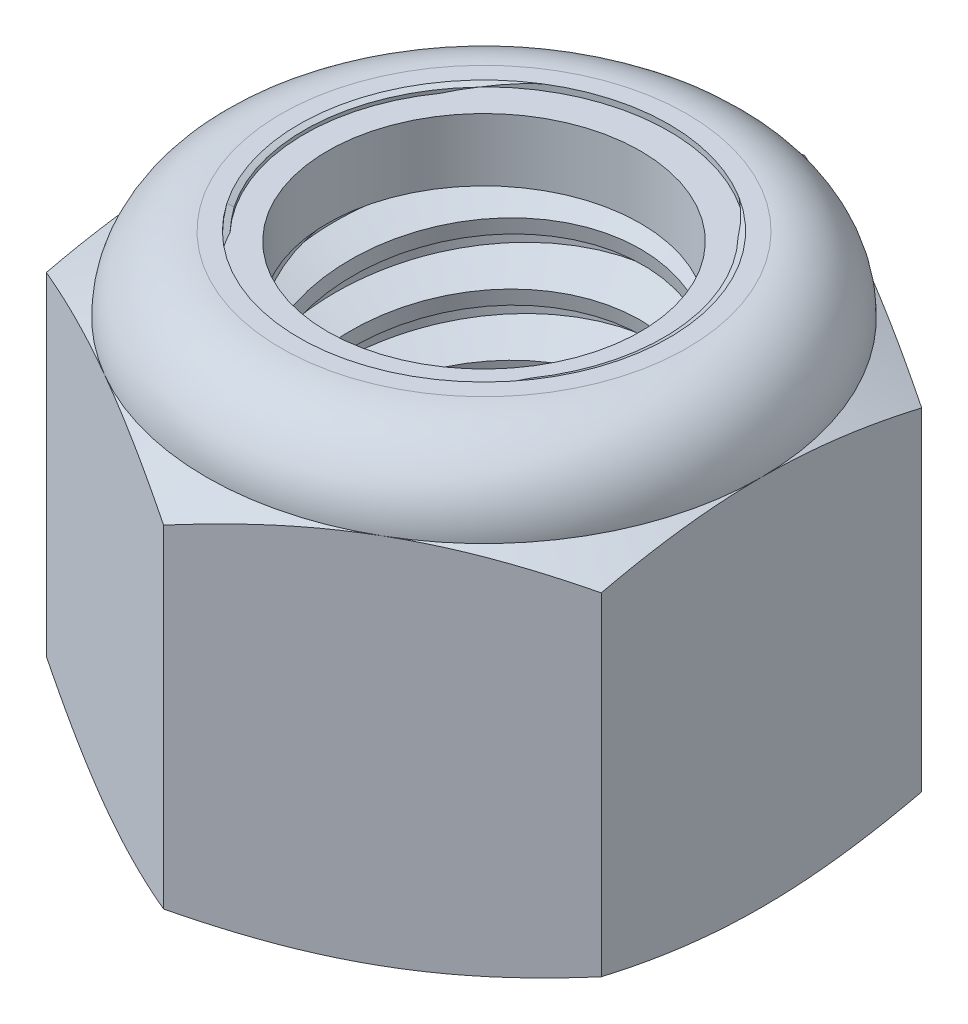
SolidWorks part; units mm, degrees
ref_plane "Front" through (0, 0, 0) normal (0, 0, 1) x (1, 0, 0)
ref_plane "Top" through (0, 0, 0) normal (0, 1, 0) x (1, 0, 0)
ref_plane "Right" through (0, 0, 0) normal (1, 0, 0) x (0, 0, -1)
sketch "Sketch1" plane through (0, 0, 0) normal (0, 1, 0) x (1, 0, 0)
  line L1 (0, 8.2489) -> (-7.1438, 4.1244)
  line L2 (-7.1438, 4.1244) -> (-7.1438, -4.1244)
  line L3 (-7.1438, -4.1244) -> (0, -8.2489)
  line L4 (0, -8.2489) -> (7.1437, -4.1244)
  line L5 (7.1437, -4.1244) -> (7.1437, 4.1244)
  line L6 (7.1437, 4.1244) -> (0, 8.2489)
  circle A0 centre (0, 0) radius 7.1438 construction
  dimension "Hex Flats" = 14.2875
extrude "Extrude1" add sketch "Sketch1" along normal blind 11.5094
sketch "Sketch2" plane through (0, 0, 0) normal (1, 0, 0) x (0, 0, -1)
  line L0 (-4.7625, 0) -> (-4.7625, 11.5094) construction
  line L1 (0, 0) -> (4.7625, 0)
  line L2 (0, 0) -> (0, 11.5094)
  line L3 (0, 11.5094) -> (4.7625, 11.5094)
  line L4 (4.7625, 0) -> (4.7625, 11.5094)
  line L5 (-4.1244, 11.5094) -> (4.1244, 11.5094) construction
  line L7 (0, -4.7625) -> (0, 0) construction
  dimension "Thread Dia" = 9.525
revolve "Revolve1" add sketch "Sketch2" angle 360 about L7
sketch "Sketch3" plane through (0, 0, 0) normal (1, 0, 0) x (0, 0, -1)
  line L0 (4.7625, 11.5094) -> (-4.7625, 11.5094) construction
  line L1 (-4.7625, 11.5094) -> (-4.7625, 9.9219) construction
  line L2 (-4.7625, 9.9219) -> (4.7625, 11.5094) construction
  line L3 (4.7625, 11.5094) -> (4.7951, 11.3136) construction
  line L4 (4.7951, 11.3136) -> (5.0235, 9.9435)
  line L5 (5.0235, 9.9435) -> (4.0944, 10.2916)
  line L6 (4.0944, 10.2916) -> (4.0291, 10.683)
  line L7 (4.0291, 10.683) -> (4.7951, 11.3136)
  line L8 (4.0617, 10.4873) -> (4.9093, 10.6286) construction
  line L9 (4.7625, 11.5094) -> (4.7625, 10.6041) construction
  line L10 (4.7625, 10.6041) -> (-4.7625, 9.0166) construction
  line L11 (-4.7625, 9.0166) -> (-4.7625, 9.9219) construction
  line L12 (-0.2832, 11.5094) -> (0.2832, 8.1113) construction
  line L13 (-4.7625, 0) -> (-4.7625, 11.5094) construction
  line L14 (0, 11.5094) -> (4.7625, 11.5094) construction
  line L15 (4.7625, 0) -> (4.7625, 11.5094) construction
  point P13 (0, 9.8103)
  dimension "D1" = 0.1984
  dimension "D2" = 0.3969
  dimension "Thread Pitch" = 1.5875
  dimension "D4" = 60
  dimension "D5" = 1.5875
revolve "Cut-Revolve1" cut sketch "Sketch3" angle 360 about L12
pattern_linear "LPattern1" count 7 spacing 1.5875 along (0, -1, 0) count 2 spacing 1.5875 along (0, 1, 0) of "Cut-Revolve1"
sketch "Sketch4" plane through (0, 0, 0) normal (1, 0, 0) x (0, 0, -1)
  line L0 (0, 11.5094) -> (4.7625, 11.5094)
  line L1 (4.7625, 11.5094) -> (4.0291, 11.1674)
  line L2 (4.0291, 11.1674) -> (4.0291, 0.342)
  line L3 (4.0291, 0.342) -> (4.7625, 0)
  line L4 (4.7625, 0) -> (0, 0)
  line L5 (0, 0) -> (0, 11.5094)
  line L6 (4.7625, 0) -> (4.7625, 11.5094) construction
  line L7 (0, 11.5094) -> (4.7625, 11.5094) construction
  line L8 (0, 0) -> (4.7625, 0) construction
  line L9 (0, 0) -> (0, 11.5094) construction
  line L10 (0, 11.5094) -> (0, 12.3186) construction
  dimension "D1" = 25
revolve "Cut-Revolve2" cut sketch "Sketch4" angle 360 about L10
combine bodies "Combine1" operation type subtract main body 112 bodies to subtract 111
sketch "Sketch5" plane through (0, 0, 0) normal (1, 0, 0) x (0, 0, -1)
  line L0 (0, 0) -> (7.1438, 0)
  line L1 (7.1438, 0) -> (8.2489, 0.5153)
  line L2 (8.2489, 0.5153) -> (8.2489, 9.0758)
  line L3 (8.2489, 9.0758) -> (7.1437, 9.5911)
  line L4 (5.2255, 11.5094) -> (5.2255, 12.7794)
  line L5 (5.2255, 12.7794) -> (9.5189, 12.7794)
  line L6 (9.5189, 12.7794) -> (9.5189, -1.27)
  line L7 (9.5189, -1.27) -> (0, -1.27)
  line L8 (0, -1.27) -> (0, 0)
  line L9 (7.1437, 9.5911) -> (7.1438, 0) construction
  line L10 (0, 0) -> (4.7625, 0) construction
  line L13 (8.2489, 4.7956) -> (9.5189, 4.7956) construction
  line L14 (8.2489, 11.5094) -> (8.2489, 0) construction
  line L15 (0, 0) -> (0, 12.7794) construction
  line L20 (0, 12.7794) -> (5.2255, 12.7794) construction
  line L22 (0, 11.5094) -> (4.7625, 11.5094) construction
  arc A0 (7.1437, 9.5911) -> (5.2255, 11.5094) centre (5.2255, 9.5911) ccw
  dimension "D1" = 25
  dimension "D2" = 1.27
  dimension "D3" = 11.5094
  dimension "D4" = 1.9182
revolve "Cut-Revolve3" cut sketch "Sketch5" angle 360 about L15
sketch "Sketch6" plane through (0, 0, 0) normal (1, 0, 0) x (0, 0, -1)
  line L0 (0, 9.5911) -> (6.9914, 9.5911)
  line L1 (5.2255, 11.357) -> (4.6273, 11.357)
  line L2 (0, 12.7794) -> (0, 9.5911)
  line L3 (4.6273, 12.7794) -> (0, 12.7794)
  line L4 (0, 12.7794) -> (5.2255, 12.7794) construction
  line L5 (0, 0) -> (0, 12.7794) construction
  line L6 (0, 12.7794) -> (0, 44.323) construction
  line L7 (4.6273, 11.357) -> (4.6273, 12.7794)
  line L8 (5.2255, 11.5094) -> (5.2255, 11.357) construction
  line L9 (4.6273, 11.357) -> (4.0291, 11.357) construction
  line L10 (4.0291, 11.357) -> (4.0291, 11.1674) construction
  arc A0 (6.9914, 9.5911) -> (5.2255, 11.357) centre (5.2255, 9.5911) ccw
  arc A1 (7.1437, 9.5911) -> (5.2255, 11.5094) centre (5.2255, 9.5911) ccw construction
  dimension "D1" = 0.1524
revolve "Cut-Revolve4" cut sketch "Sketch6" angle 360 about L6
sketch "Sketch7" plane through (0, 0, 0) normal (1, 0, 0) x (0, 0, -1)
  line L0 (4.0291, 9.6673) -> (6.9134, 9.6673)
  line L1 (5.2255, 11.2808) -> (4.0291, 11.2808)
  line L2 (4.0291, 11.2808) -> (4.0291, 9.6673)
  line L3 (4.0291, 9.6673) -> (0, 9.6673) construction
  line L4 (0, 9.6673) -> (0, 11.2808) construction
  line L5 (0, 11.2808) -> (4.0291, 11.2808) construction
  line L6 (4.0291, 9.6673) -> (4.0291, 9.5911) construction
  line L7 (0, 9.5911) -> (6.9914, 9.5911) construction
  line L8 (5.2255, 11.2808) -> (5.2255, 11.357) construction
  arc A0 (6.9134, 9.6673) -> (5.2255, 11.2808) centre (5.2255, 9.5911) ccw
  arc A2 (6.9914, 9.5911) -> (5.2255, 11.357) centre (5.2255, 9.5911) ccw construction
  dimension "D1" = 0.0762
revolve "Revolve2" add sketch "Sketch7" angle 360 about L4
equation "\"D1@Sketch3\"=\"Thread Pitch@Sketch3\"/8"
equation "\"D2@Sketch3\"=\"Thread Pitch@Sketch3\"/4"
equation "\"D5@Sketch3\"=\"Thread Pitch@Sketch3\""
equation "\"D4@LPattern1\"=\"Thread Pitch@Sketch3\""
equation "\"D3@LPattern1\"=\"Thread Pitch@Sketch3\""
equation "\"D1@LPattern1\"=\"Height@Extrude1\"/\"Thread Pitch@Sketch3\""
equation "\"D4@Sketch5\"=\"Height@Extrude1\"/6"
